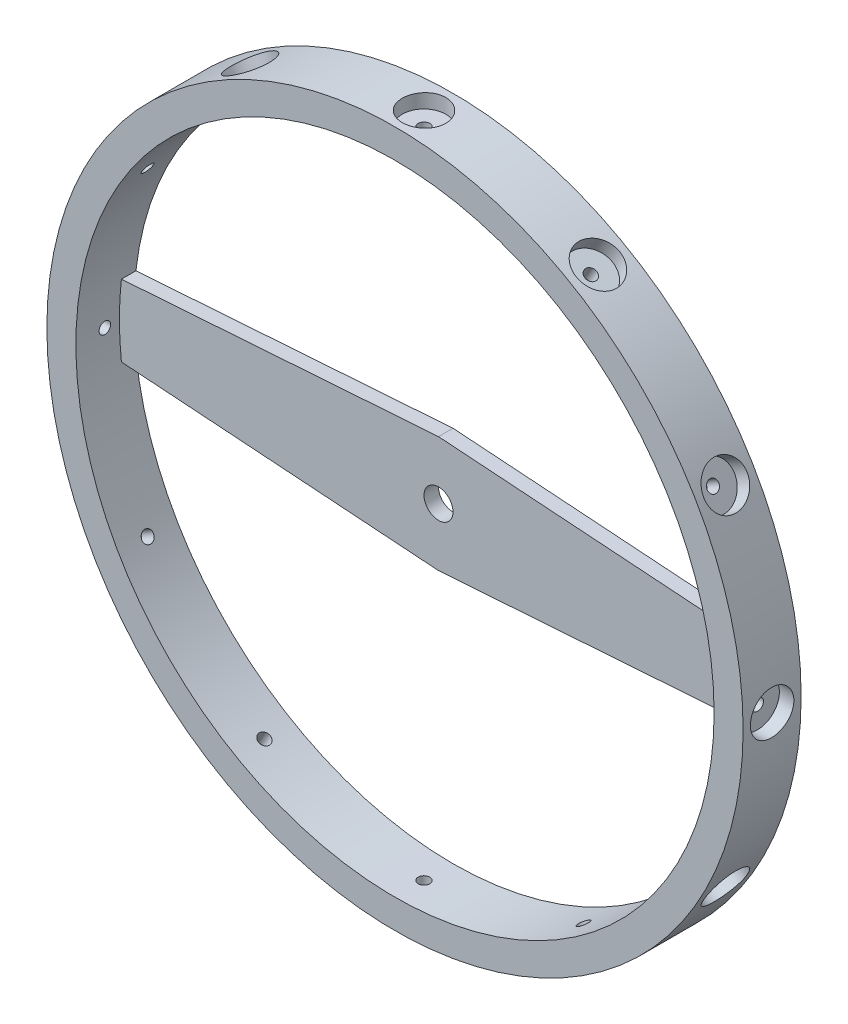
SolidWorks part; units mm, degrees
ref_plane "Front Plane" through (0, 0, 0) normal (0, 0, 1) x (1, 0, 0)
ref_plane "Top Plane" through (0, 0, 0) normal (0, 1, 0) x (1, 0, 0)
ref_plane "Right Plane" through (0, 0, 0) normal (1, 0, 0) x (0, 0, -1)
sketch "Croquis1" plane through (0, 0, 0) normal (0, 0, 1) x (1, 0, 0)
  circle A0 centre (0, 0) radius 6
  circle A1 centre (0, 0) radius 5.5
  dimension "D1" = 12
  dimension "D2" = 11
extrude "Saliente-Extruir1" add sketch "Croquis1" along normal blind 1
sketch "Croquis5" plane through (0, 0, 0) normal (0, 0, 1) x (1, 0, 0)
  line L0 (0, 0) -> (8.2712, 0) construction
  line L4 (0, 1) -> (0, -1)
  line L5 (0, -1) -> (5.4652, -0.6178)
  line L6 (0, 1) -> (5.4652, 0.6178)
  circle A0 centre (0, 0) radius 5.5 construction
  arc A2 (5.4652, -0.6178) -> (5.4652, 0.6178) centre (0, 0) ccw
  point P0 (0, 0)
  dimension "D3" = 4
  dimension "D1" = 2
  dimension "D4" = 4
extrude "Saliente-Extruir2" add sketch "Croquis5" along normal blind 0.25
mirror "Simetría1" of "Saliente-Extruir2"
ref_plane "Plano2" through (0, 6, 0) normal (0, 1, 0) x (-1, 0, 0)
sketch "Croquis8" plane through (0, 6, 0) normal (0, 1, 0) x (-1, 0, 0)
  circle A0 centre (0, 0.5) radius 0.1
  dimension "D2" = 0.2
  dimension "D1" = 0.5
extrude "Cortar-Extruir4" cut sketch "Croquis8" against normal blind 1
sketch "Croquis9" plane through (0, 6, 0) normal (0, 1, 0) x (-1, 0, 0)
  circle A0 centre (0, 0.5) radius 0.375
  dimension "D1" = 0.75
extrude "Cortar-Extruir5" cut sketch "Croquis9" against normal blind 0.25
pattern_circular "MatrizC7" count 12 over 360 about axis through (0, 0, 0) along (0, 0, 1) of "Cortar-Extruir4", "Cortar-Extruir5"
sketch "Croquis10" plane through (0, 0, 0) normal (0, 0, -1) x (-1, 0, 0)
  circle A0 centre (0, 0) radius 0.25
  dimension "D1" = 0.5
extrude "Cortar-Extruir6" cut sketch "Croquis10" against normal blind 10
